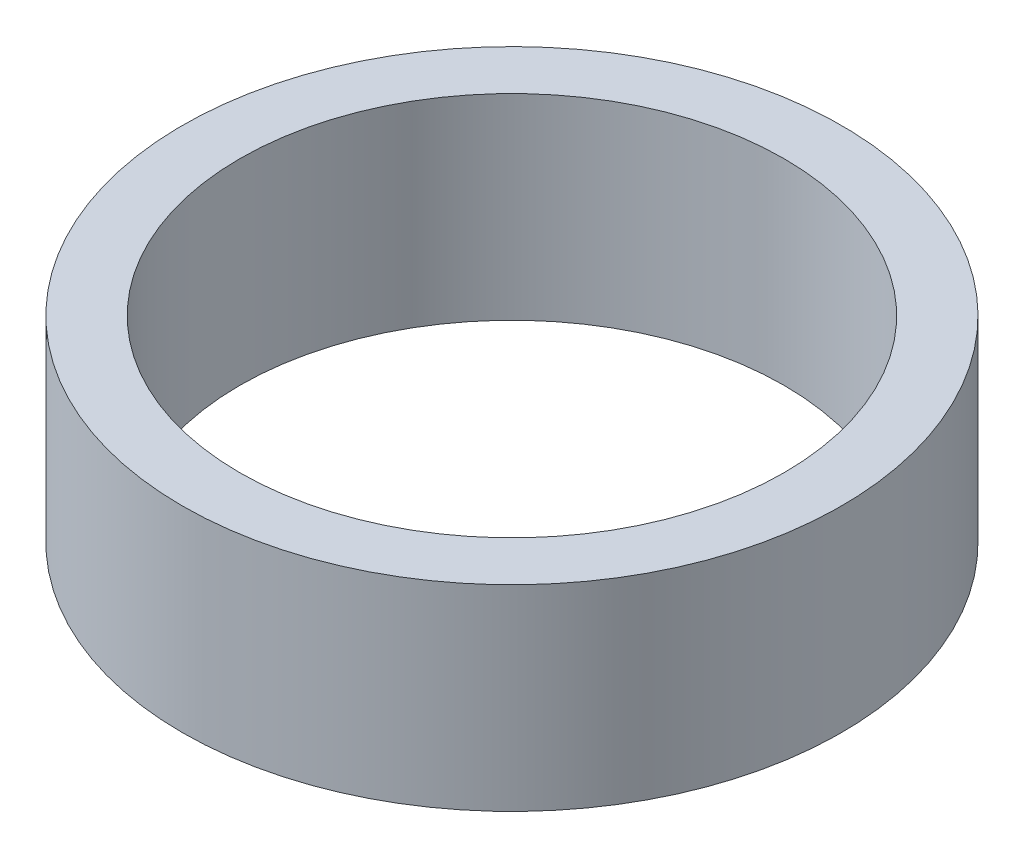
SolidWorks part; units mm, degrees
ref_plane "Front Plane" through (0, 0, 0) normal (0, 0, 1) x (1, 0, 0)
ref_plane "Top Plane" through (0, 0, 0) normal (0, 1, 0) x (1, 0, 0)
ref_plane "Right Plane" through (0, 0, 0) normal (1, 0, 0) x (0, 0, -1)
sketch "Sketch1" plane through (0, 0, 0) normal (0, 1, 0) x (1, 0, 0)
  circle A0 centre (0, 0) radius 23.5
  circle A1 centre (0, 0) radius 19.4
  dimension "D1" = 47
  dimension "D2" = 38.8
extrude "Boss-Extrude1" add sketch "Sketch1" along normal blind 14
